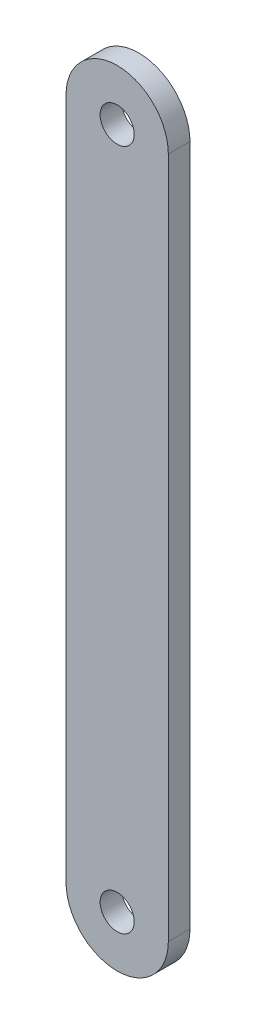
SolidWorks part; units mm, degrees
ref_plane "Plano frontal" through (0, 0, 0) normal (0, 0, 1) x (1, 0, 0)
ref_plane "Plano superior" through (0, 0, 0) normal (0, 1, 0) x (1, 0, 0)
ref_plane "Plano direito" through (0, 0, 0) normal (1, 0, 0) x (0, 0, -1)
sketch "Esboço1" plane through (0, 0, 0) normal (0, 0, 1) x (1, 0, 0)
  line L0 (0, 0) -> (0, 200) construction
  line L1 (-15, 0) -> (-15, 200)
  line L2 (15, 0) -> (15, 200)
  arc A0 (-15, 0) -> (15, 0) centre (0, 0) ccw
  arc A1 (15, 200) -> (-15, 200) centre (0, 200) ccw
  circle A2 centre (0, 200) radius 5
  circle A3 centre (0, 0) radius 5
  point P3 (0, 100)
  dimension "D1" = 30
  dimension "D3" = 10
  dimension "D2" = 200
extrude "Ressalto-extrusão1" add sketch "Esboço1" along normal blind 6.35
